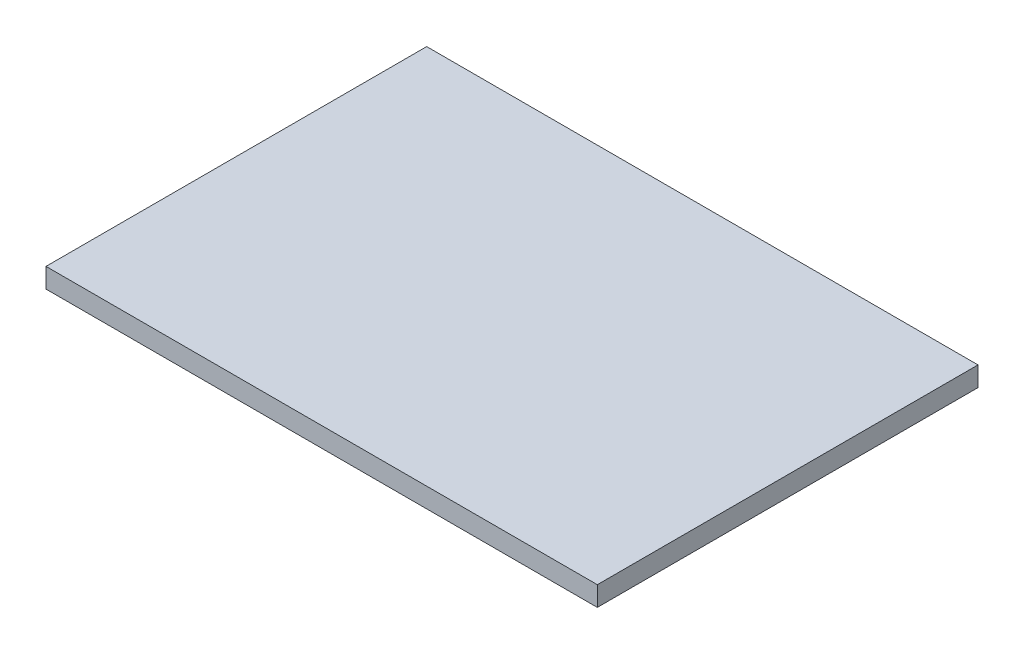
SolidWorks part; units mm, degrees
ref_plane "Front Plane" through (0, 0, 0) normal (0, 0, 1) x (1, 0, 0)
ref_plane "Top Plane" through (0, 0, 0) normal (0, 1, 0) x (1, 0, 0)
ref_plane "Right Plane" through (0, 0, 0) normal (1, 0, 0) x (0, 0, -1)
sketch "Sketch1" plane through (0, 0, 0) normal (0, 1, 0) x (1, 0, 0)
  line L1 (-533.4, -368.3) -> (533.4, -368.3)
  line L2 (-533.4, -368.3) -> (-533.4, 368.3)
  line L3 (-533.4, 368.3) -> (533.4, 368.3)
  line L4 (533.4, -368.3) -> (533.4, 368.3)
  line L5 (-533.4, -368.3) -> (533.4, 368.3) construction
  line L6 (-533.4, 368.3) -> (533.4, -368.3) construction
  point P0 (0, 0)
  dimension "D1" = 1066.8
  dimension "D2" = 736.6
extrude "Boss-Extrude1" add sketch "Sketch1" along normal blind 38.1
sketch "Sketch2" plane through (0, 38.1, 0) normal (0, 1, 0) x (1, 0, 0)
  line L1 (-381, -228.6) -> (381, -228.6)
  line L2 (-381, -228.6) -> (-381, 228.6)
  line L3 (-381, 228.6) -> (381, 228.6)
  line L4 (381, -228.6) -> (381, 228.6)
  line L5 (-381, -228.6) -> (381, 228.6) construction
  line L6 (-381, 228.6) -> (381, -228.6) construction
  point P0 (0, 0)
  dimension "D1" = 762
  dimension "D2" = 457.2
